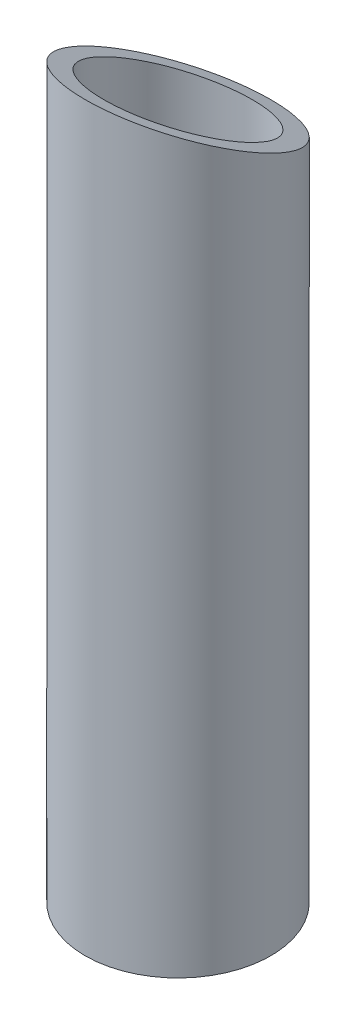
SolidWorks part; units mm, degrees
ref_plane "Front Plane" through (0, 0, 0) normal (0, 0, 1) x (1, 0, 0)
ref_plane "Top Plane" through (0, 0, 0) normal (0, 1, 0) x (1, 0, 0)
ref_plane "Right Plane" through (0, 0, 0) normal (1, 0, 0) x (0, 0, -1)
sketch "Sketch1" plane through (0, 0, 0) normal (0, 1, 0) x (1, 0, 0)
  circle A0 centre (0, 0) radius 15.9
  circle A1 centre (0, 0) radius 12.725
  dimension "D1" = 3.175
extrude "Boss-Extrude1" add sketch "Sketch1" along normal blind 127
sketch "Sketch2" plane through (0, 0, 0) normal (1, 0, 0) x (0, 0, -1)
  line L0 (15.9, 127) -> (-15.9, 127)
  line L1 (-15.9, 127) -> (15.9, 111.1)
  line L2 (15.9, 0) -> (15.9, 127) construction
  line L3 (15.9, 111.1) -> (15.9, 127)
extrude "Cut-Extrude1" cut sketch "Sketch2" against normal through all and the other way through all
